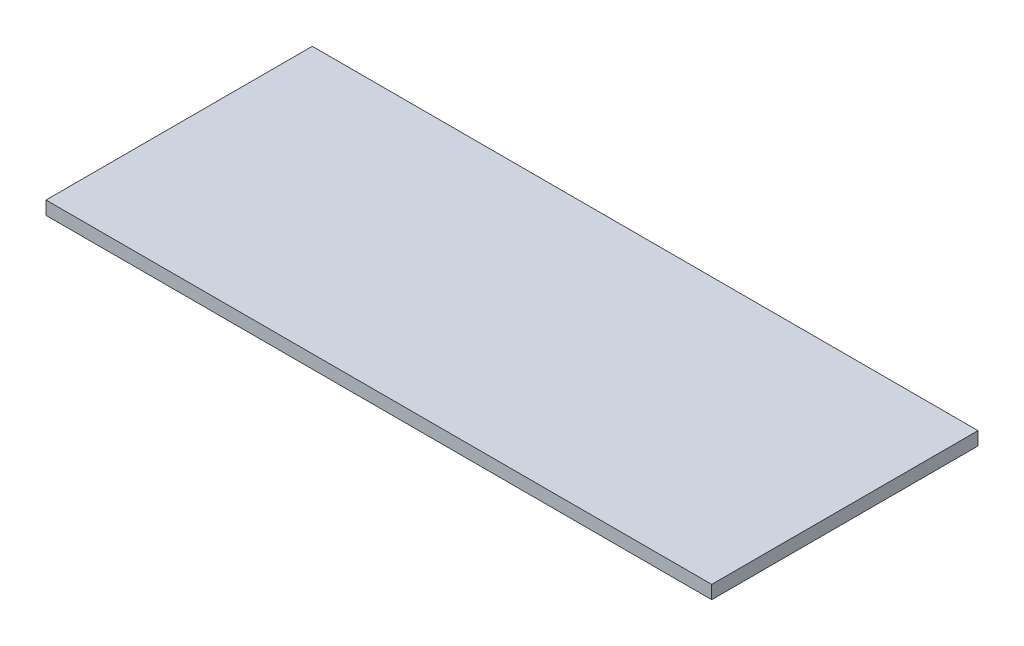
SolidWorks part; units mm, degrees
material "Pine"
ref_plane "Front Plane" through (0, 0, 0) normal (0, 0, 1) x (1, 0, 0)
ref_plane "Top Plane" through (0, 0, 0) normal (0, 1, 0) x (1, 0, 0)
ref_plane "Right Plane" through (0, 0, 0) normal (1, 0, 0) x (0, 0, -1)
sketch "Sketch1" plane through (0, 0, 0) normal (0, 1, 0) x (1, 0, 0)
  line L1 (250, -100) -> (-250, -100)
  line L2 (250, -100) -> (250, 100)
  line L3 (250, 100) -> (-250, 100)
  line L4 (-250, -100) -> (-250, 100)
  line L5 (250, -100) -> (-250, 100) construction
  line L6 (250, 100) -> (-250, -100) construction
  point P0 (0, 0)
  dimension "D1" = 200
  dimension "D2" = 500
extrude "Boss-Extrude1" add sketch "Sketch1" along normal blind 10
